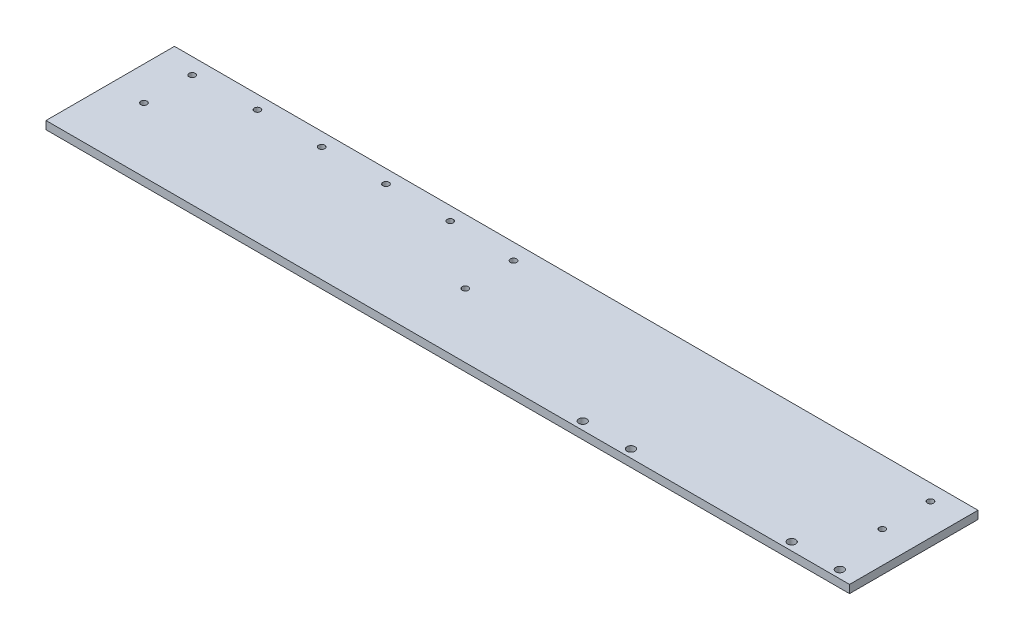
SolidWorks part; units mm, degrees
material "PC High Viscosity"
ref_plane "Front Plane" through (0, 0, 0) normal (0, 0, 1) x (1, 0, 0)
ref_plane "Top Plane" through (0, 0, 0) normal (0, 1, 0) x (1, 0, 0)
ref_plane "Right Plane" through (0, 0, 0) normal (1, 0, 0) x (0, 0, -1)
sketch "Sketch1" plane through (0, 0, 0) normal (0, 1, 0) x (1, 0, 0)
  line L0 (88.9, 50.7635) -> (88.9, -50.7635) construction
  line L1 (317.5, -50.7635) -> (-317.5, -50.7635)
  line L2 (317.5, -50.7635) -> (317.5, 50.7635)
  line L3 (317.5, 50.7635) -> (-317.5, 50.7635)
  line L4 (-317.5, -50.7635) -> (-317.5, 50.7635)
  line L5 (317.5, -50.7635) -> (-317.5, 50.7635) construction
  line L6 (317.5, 50.7635) -> (-317.5, -50.7635) construction
  circle A0 centre (-290.83, 38.0635) radius 2.4638
  circle A1 centre (-290.83, -0.0365) radius 2.4638
  circle A2 centre (292.608, 0.0365) radius 2.4638
  circle A3 centre (292.608, 38.0635) radius 2.4638
  circle A4 centre (-241.3, 40.0955) radius 2.4638
  circle A5 centre (-36.83, 38.0635) radius 2.4638
  circle A6 centre (-36.83, -0.0365) radius 2.4638
  circle A7 centre (100.33, -44.4135) radius 3.175
  circle A8 centre (138.43, -44.4135) radius 3.175
  circle A9 centre (303.53, -44.4135) radius 3.175
  circle A10 centre (265.43, -44.4135) radius 3.175
  circle A11 centre (-190.5, 40.0955) radius 2.4638
  circle A12 centre (-139.7, 40.0955) radius 2.4638
  circle A13 centre (-88.9, 40.0955) radius 2.4638
  point P0 (0, 0)
  dimension "D11" = 4.9276
  dimension "D8" = 38.1
  dimension "D12" = 4.9276
  dimension "D14" = 6.35
  dimension "D20" = 4.9276
  dimension "D24" = 50.8
  dimension "D1" = 635
  dimension "D2" = 101.527
  dimension "D3" = 38.027
  dimension "D4" = 38.1
  dimension "D5" = 26.67
  dimension "D6" = 12.7
  dimension "D7" = 24.892
  dimension "D9" = 12.7
  dimension "D10" = 12.7
  dimension "D13" = 254
  dimension "D15" = 13.97
  dimension "D16" = 38.1
  dimension "D17" = 127
  dimension "D18" = 38.1
  dimension "D19" = 6.35
  dimension "D21" = 76.2
  dimension "D22" = 50.8
  dimension "D23" = 10.668
  dimension "D25" = 50.8
  dimension "D26" = 228.6
extrude "Boss-Extrude1" add sketch "Sketch1" along normal blind 6.35
